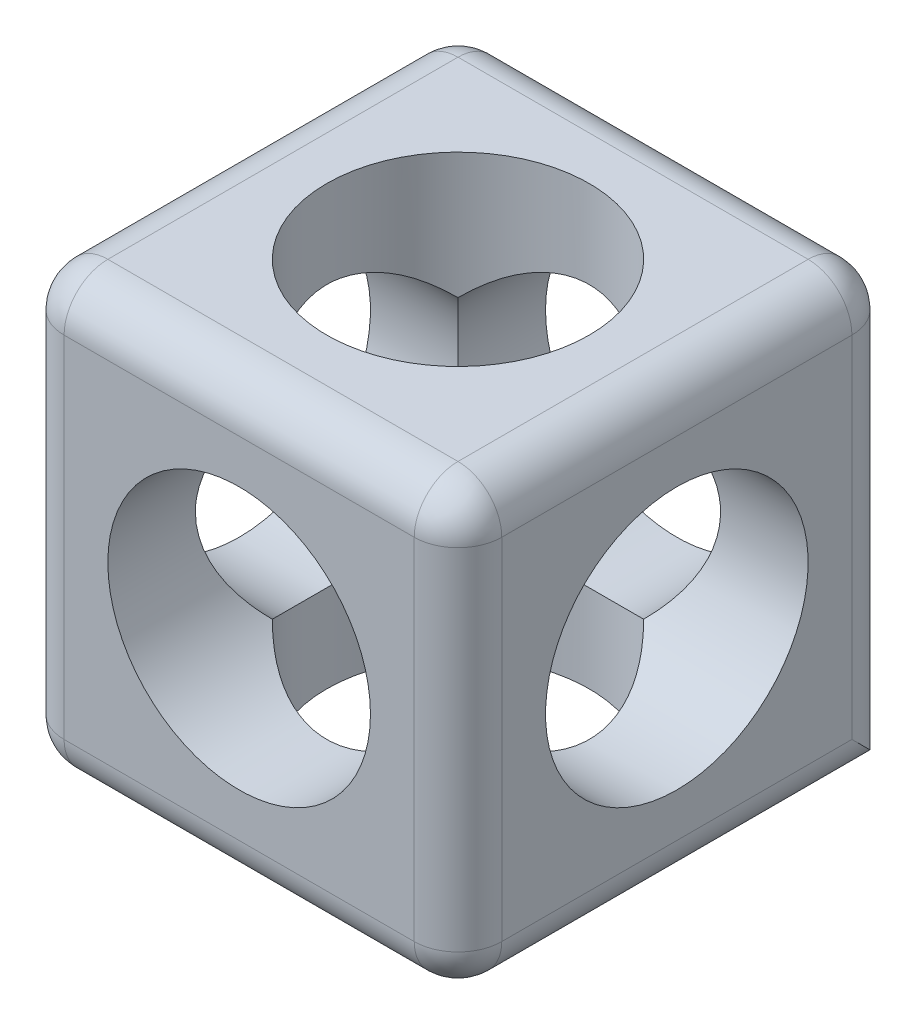
SolidWorks part; units mm, degrees
ref_plane "Plan de face" through (0, 0, 0) normal (0, 0, 1) x (1, 0, 0)
ref_plane "Plan de dessus" through (0, 0, 0) normal (0, 1, 0) x (1, 0, 0)
ref_plane "Plan de droite" through (0, 0, 0) normal (1, 0, 0) x (0, 0, -1)
sketch "Esquisse1" plane through (0, 0, 0) normal (0, 0, 1) x (1, 0, 0)
  line L1 (0, 0) -> (-1, 0)
  line L2 (0, 0) -> (0, 1)
  line L3 (0, 1) -> (-1, 1)
  line L4 (-1, 0) -> (-1, 1)
  dimension "D1" = 1
  dimension "D2" = 1
extrude "Boss.-Extru.1" add sketch "Esquisse1" along normal blind 1
sketch "Esquisse2" plane through (0, 0, 0) normal (1, 0, 0) x (0, 0, -1)
  circle A0 centre (-0.5, 0.5) radius 0.3
extrude "Enlèv. mat.-Extru.1" cut sketch "Esquisse2" against normal blind 1 contours A0
sketch "Esquisse3" plane through (0, 1, 0) normal (0, 1, 0) x (1, 0, 0)
  circle A0 centre (-0.5, -0.5) radius 0.3
sketch "Esquisse4" plane through (0, 0, 0) normal (0, 0, -1) x (-1, 0, 0)
  circle A0 centre (0.5, 0.5) radius 0.3
extrude "Enlèv. mat.-Extru.2" cut sketch "Esquisse4" against normal blind 1 contours A0
extrude "Enlèv. mat.-Extru.3" cut sketch "Esquisse3" against normal blind 1 contours A0
fillet "Congé2" radius 0.1 3 edges at (-0.5, 1, 1) (-1, 0.5, 1) (-1, 1, 0.5)
fillet "Congé3" radius 0.1 11 edges at (-1, 0.45, 0) (-0.9707, 0.9707, 0) (0, 0.9707, 0.9707) (-1, 0, 0.45) (-0.9707, 0, 0.9707) (-0.45, 1, 0) (0, 0.5, 0) (0, 1, 0.45) (0, 0.45, 1) (0, 0, 0.5) (-0.45, 0, 1)
